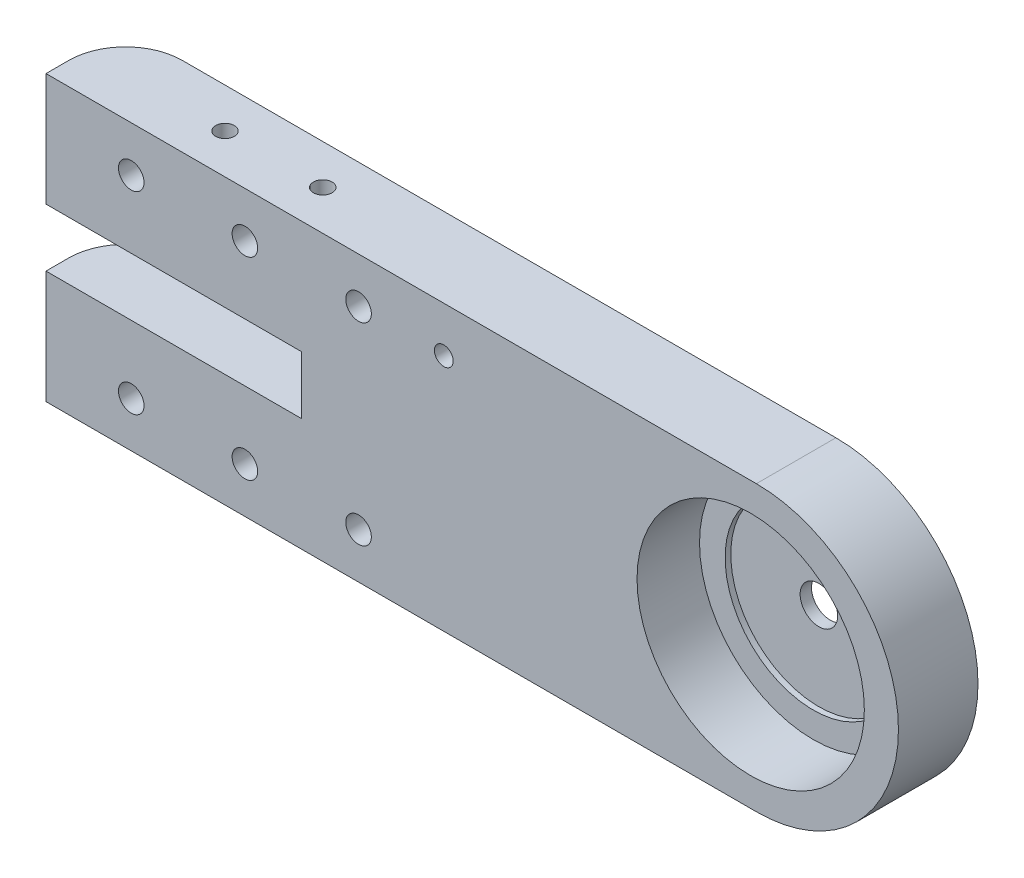
SolidWorks part; units mm, degrees
ref_plane "Front Plane" through (0, 0, 0) normal (0, 0, 1) x (1, 0, 0)
ref_plane "Top Plane" through (0, 0, 0) normal (0, 1, 0) x (1, 0, 0)
ref_plane "Right Plane" through (0, 0, 0) normal (1, 0, 0) x (0, 0, -1)
ref_plane "Plane1" through (0, 0, 14) normal (0, 0, 1) x (1, 0, 0)
sketch "Sketch1" plane through (0, 0, 14) normal (0, 0, 1) x (1, 0, 0)
  line L0 (125, 0) -> (0, 0)
  line L1 (0, 0) -> (0, -50)
  line L2 (0, -50) -> (125, -50)
  arc A0 (125, -50) -> (125, 0) centre (125, -25) ccw
extrude "Boss-Extrude1" add sketch "Sketch1" against normal blind 14
sketch "Sketch2" plane through (0, 0, 0) normal (0, 0, -1) x (-1, 0, 0)
  line L0 (0, -30.1) -> (0, -19.9)
  line L1 (0, -19.9) -> (-45, -19.9)
  line L2 (-45, -19.9) -> (-45, -30.1)
  line L3 (-45, -30.1) -> (0, -30.1)
extrude "Cut-Extrude1" cut sketch "Sketch2" against normal through all
ref_plane "Plane2" through (0, -25, 0) normal (0, 1, 0) x (1, 0, 0)
sketch "Sketch3" plane through (0, -25, 0) normal (0, 1, 0) x (1, 0, 0)
  line L0 (127.3, 0) -> (124, 0)
  line L1 (124, 0) -> (124, -14)
  line L2 (124, -14) -> (144, -14)
  line L3 (144, -14) -> (144, -3)
  line L4 (144, -3) -> (139.5, -3)
  line L5 (139.5, -3) -> (139.5, -2)
  line L6 (139.5, -2) -> (127.3, -2)
  line L7 (127.3, -2) -> (127.3, 0)
  line L8 (124, 0) -> (124, -14) construction
revolve "Cut-Revolve1" cut sketch "Sketch3" angle 360 about L8
hole_wizard "#4 Clearance Hole1" positions "Sketch5" profile "Sketch4" hole size "#4" standard "ANSI Inch"
sketch "Sketch5" plane through (0, 0, 0) normal (0, 0, -1) x (-1, 0, 0)
  point P0 (-70, -8)
sketch "Sketch4" plane through (70, -8, 0) normal (1, 0, 0) x (0, 1, 0)
  line L0 (0, 0) -> (0, 14)
  line L1 (0, 14) -> (1.65, 14)
  line L2 (1.65, 14) -> (1.65, 0)
  line L5 (1.65, 0) -> (0, 0)
  line L11 (0, -6.35) -> (0, 107.95) construction
  dimension "Thru Hole Dia." = 3.3
  dimension "Thru Hole Depth" = 14
hole_wizard "#4 Clearance Hole2" positions "Sketch7" profile "Sketch6" hole size "#4" standard "ANSI Inch"
sketch "Sketch7" plane through (0, 0, 0) normal (0, 1, 0) x (1, 0, 0)
  point P0 (24.5, -7)
  point P1 (41.7, -7)
sketch "Sketch6" plane through (24.5, 0, 7) normal (1, 0, 0) x (0, 0, 1)
  line L0 (0, 0) -> (0, 19.9)
  line L1 (0, 19.9) -> (1.65, 19.9)
  line L2 (1.65, 19.9) -> (1.65, 0)
  line L5 (1.65, 0) -> (0, 0)
  line L11 (0, -6.35) -> (0, 107.95) construction
  dimension "Thru Hole Dia." = 3.3
  dimension "Thru Hole Depth" = 19.9
hole_wizard "#8 Clearance Hole1" positions "Sketch9" profile "Sketch8" hole size "#8" standard "ANSI Inch"
sketch "Sketch9" plane through (0, 0, 0) normal (0, 0, -1) x (-1, 0, 0)
  point P0 (-15, -8)
  point P1 (-15, -42)
  point P2 (-35, -42)
  point P3 (-35, -8)
  point P4 (-55, -8)
  point P5 (-55, -42)
sketch "Sketch8" plane through (15, -8, 0) normal (1, 0, 0) x (0, 1, 0)
  line L0 (0, 0) -> (0, 14)
  line L1 (0, 14) -> (2.25, 14)
  line L2 (2.25, 14) -> (2.25, 0)
  line L5 (2.25, 0) -> (0, 0)
  line L11 (0, -6.35) -> (0, 107.95) construction
  dimension "Thru Hole Dia." = 4.5
  dimension "Thru Hole Depth" = 14
chamfer "Chamfer1" distance 2.45 angle 45 6 edges at (52.75, -42, 0) (52.75, -8, 0) (12.75, -42, 0) (32.75, -42, 0) (12.75, -8, 0) (32.75, -8, 0)
fillet "Fillet1" radius 10 2 edges at (0, -40.05, 0) (0, -9.95, 0)
